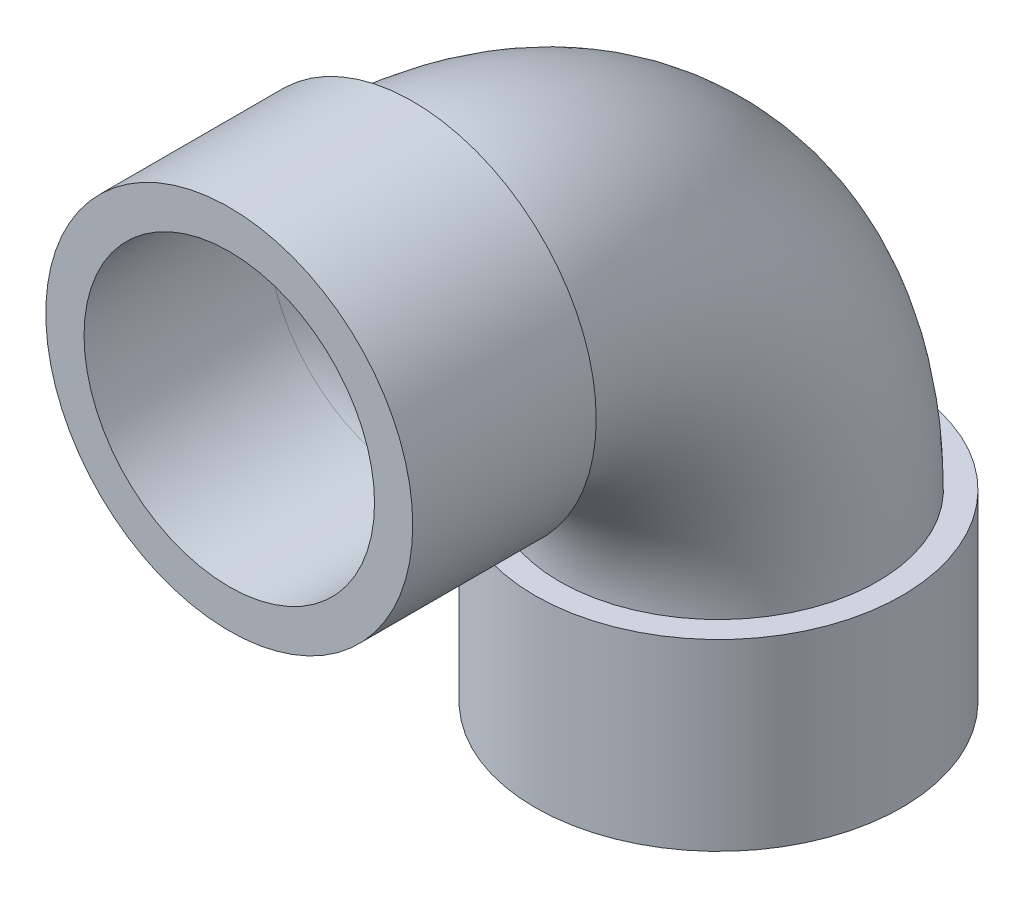
SolidWorks part; units mm, degrees
material "ABS"
ref_plane "Front Plane" through (0, 0, 0) normal (0, 0, 1) x (1, 0, 0)
ref_plane "Top Plane" through (0, 0, 0) normal (0, 1, 0) x (1, 0, 0)
ref_plane "Right Plane" through (0, 0, 0) normal (1, 0, 0) x (0, 0, -1)
sketch "Sketch1" plane through (0, 0, 0) normal (0, 1, 0) x (1, 0, 0)
  circle A0 centre (0, 0) radius 30.1625
  circle A1 centre (0, 0) radius 38.1
  dimension "D1" = 60.325
  dimension "D2" = 76.2
extrude "Boss-Extrude1" add sketch "Sketch1" along normal blind 38.1
sketch "Sketch3" plane through (0, 0, 0) normal (1, 0, 0) x (0, 0, -1)
  line L1 (38.1, 38.1) -> (-38.1, 38.1) construction
  line L2 (0, 0) -> (0, 38.1) construction
  line L3 (-38.1, 38.1) -> (-38.1, 0) construction
  arc A0 (0, 38.1) -> (-63.5, 101.6) centre (-63.5, 38.1) ccw
  dimension "D1" = 25.4
ref_plane "Plane1" through (0, 0, 63.5) normal (0, 0, 1) x (1, 0, 0)
sketch "Sketch4" plane through (0, 0, 63.5) normal (0, 0, 1) x (1, 0, 0)
  line L1 (0, 38.1) -> (0, 101.6) construction
  line L3 (38.1, 38.1) -> (-38.1, 38.1) construction
  circle A0 centre (0, 101.6) radius 38.1
  circle A1 centre (0, 101.6) radius 30.1625
  dimension "D2" = 76.2
  dimension "D3" = 60.325
  dimension "D1" = 63.5
extrude "Boss-Extrude2" add sketch "Sketch4" along normal blind 38.1 separate body
sketch "Sketch6" plane through (0, 38.1, 0) normal (0, 1, 0) x (1, 0, 0)
  circle A0 centre (0, 0) radius 30.1625 construction
  circle A1 centre (0, 0) radius 30.1625
  circle A2 centre (0, 0) radius 33.02
  dimension "D1" = 66.04
sweep "Sweep2" add profiles "Sketch6" path "Sketch3"
